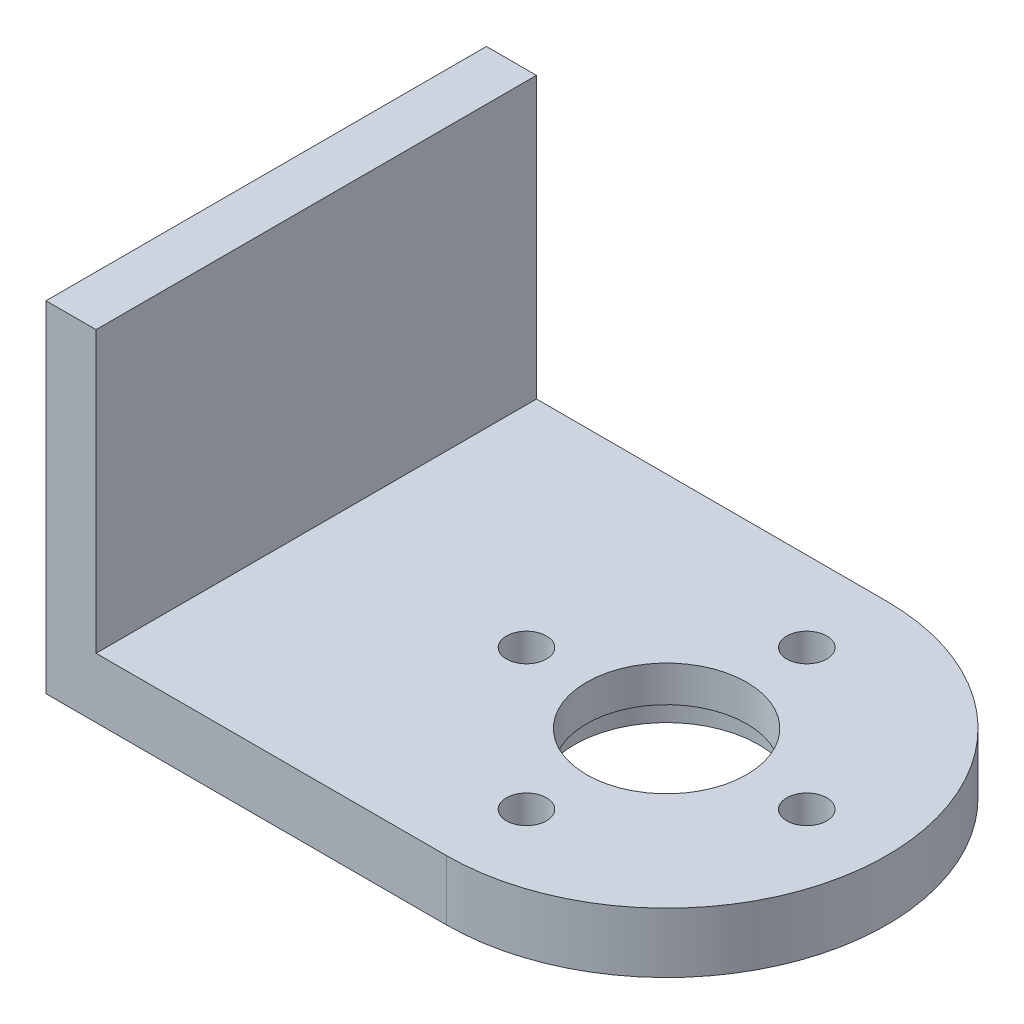
SolidWorks part; units mm, degrees
ref_plane "Front Plane" through (0, 0, 0) normal (0, 0, 1) x (1, 0, 0)
ref_plane "Top Plane" through (0, 0, 0) normal (0, 1, 0) x (1, 0, 0)
ref_plane "Right Plane" through (0, 0, 0) normal (1, 0, 0) x (0, 0, -1)
sketch "Sketch1" plane through (0, 0, 0) normal (0, 1, 0) x (1, 0, 0)
  line L0 (-28.2208, 0) -> (26.2745, 0) construction
  line L2 (-14, -11) -> (-14, 11)
  line L5 (-14, 11) -> (6, 11)
  line L6 (6, -11) -> (-14, -11)
  circle A0 centre (6, -7) radius 1
  circle A1 centre (-1, 0) radius 1
  circle A2 centre (6, 0) radius 4
  arc A3 (6, -11) -> (6, 11) centre (6, 0) ccw
  circle A4 centre (13, 0) radius 1
  circle A5 centre (6, 7) radius 1
  point P0 (0, 0)
  point P6 (-14, 0)
  point P22 (6, 0)
  dimension "D3" = 8
  dimension "D5" = 22
  dimension "D6" = 4
  dimension "D12" = 2
  dimension "D2" = 22
  dimension "D4" = 20
  dimension "D11" = 7
extrude "Boss-Extrude1" add sketch "Sketch1" along normal blind 3
sketch "Sketch2" plane through (0, 3, 0) normal (0, 1, 0) x (1, 0, 0)
  line L0 (-14, 11) -> (-11.5, 11)
  line L1 (6, 11) -> (-14, 11) construction
  line L2 (-11.5, 11) -> (-11.5, -11)
  line L3 (-14, -11) -> (6, -11) construction
  line L4 (-11.5, -11) -> (-14, -11)
  line L5 (-14, 11) -> (-14, -11)
  dimension "D1" = 2.5
extrude "Boss-Extrude2" add sketch "Sketch2" along normal blind 14
sketch "Sketch3" plane through (-11.5, 0, 0) normal (1, 0, 0) x (0, 0, -1)
  line L0 (11, 17) -> (11, 3) construction
  line L1 (-11, 17) -> (11, 17) construction
  line L2 (-11, 17) -> (-11, 3) construction
  circle A0 centre (6.9, 14) radius 1.1324
  circle A1 centre (-6.9, 14) radius 1.131
  point P6 (11, 10)
  point P11 (-11, 10)
  dimension "D1" = 4.1
  dimension "D2" = 3
  dimension "D3" = 4.1
  dimension "D4" = 3
sketch "Sketch4" plane through (0, 0, 0) normal (0, -1, 0) x (1, 0, 0)
  circle A0 centre (6, 0) radius 4.6
  dimension "D1" = 9.2
extrude "Cut-Extrude2" cut sketch "Sketch4" against normal blind 1.2
sketch "Sketch5" plane through (0, 0, 0) normal (0, -1, 0) x (1, 0, 0)
  circle A0 centre (13, 0) radius 1.9
  circle A1 centre (6, -7) radius 1.9
  circle A2 centre (-1, 0) radius 1.9
  circle A3 centre (6, 7) radius 1.9
  point P12 (6, 0)
  dimension "D1" = 3.8
  dimension "D2" = 4
extrude "Cut-Extrude3" cut sketch "Sketch5" against normal blind 1.5
sketch "Sketch6" plane through (-14, 0, 0) normal (-1, 0, 0) x (0, 0, 1)
  line L3 (-11, 17) -> (-11, 0) construction
  line L4 (-11, 0) -> (11, 0) construction
  line L5 (11, 17) -> (11, 0) construction
  circle A0 centre (-5.55, 13.75) radius 1
  circle A1 centre (5.55, 13.75) radius 1
  dimension "D3" = 2
  dimension "D6" = 2
  dimension "D1" = 5.45
  dimension "D2" = 13.75
  dimension "D4" = 5.45
  dimension "D5" = 13.75
